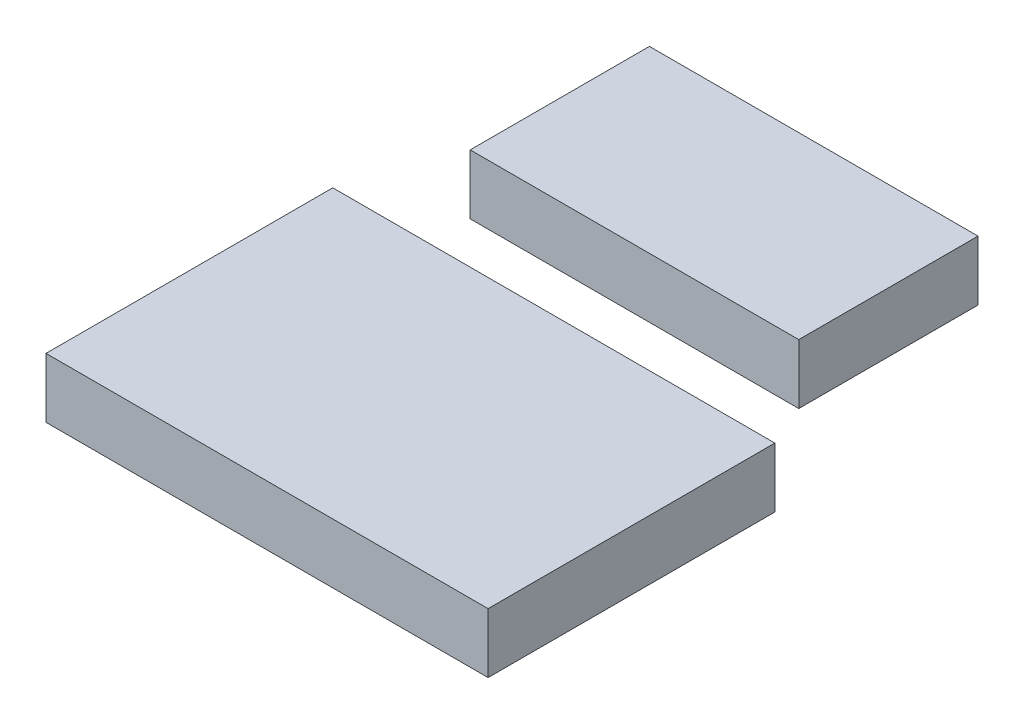
SolidWorks part; units mm, degrees
ref_plane "Front Plane" through (0, 0, 0) normal (0, 0, 1) x (1, 0, 0)
ref_plane "Top Plane" through (0, 0, 0) normal (0, 1, 0) x (1, 0, 0)
ref_plane "Right Plane" through (0, 0, 0) normal (1, 0, 0) x (0, 0, -1)
sketch "Sketch1" plane through (0, 0, 0) normal (0, 1, 0) x (1, 0, 0)
  line L0 (-31, 0.5) -> (-37, 0.5)
  line L1 (-37, 47.5) -> (37, 47.5)
  line L2 (-37, 47.5) -> (-37, -47.5)
  line L3 (-37, -47.5) -> (37, -47.5)
  line L4 (37, 47.5) -> (37, -47.5)
  line L5 (-37, 47.5) -> (37, -47.5) construction
  line L6 (-37, -47.5) -> (37, 47.5) construction
  line L7 (-31, 47.5) -> (24, 47.5)
  line L8 (-31, 47.5) -> (-31, 0.5)
  line L9 (-31, 0.5) -> (24, 0.5)
  line L10 (24, 47.5) -> (24, 0.5)
  line L11 (-31, 47.5) -> (24, 47.5)
  line L12 (-31, 47.5) -> (-31, 17.5)
  line L13 (-31, 17.5) -> (24, 17.5)
  line L14 (24, 47.5) -> (24, 17.5)
  line L15 (24, 0.5) -> (37, 0.5)
  point P0 (0, 0)
  dimension "D1" = 95
  dimension "D2" = 74
  dimension "D3" = 48
  dimension "D4" = 55
  dimension "D5" = 6
  dimension "D6" = 30
extrude "Boss-Extrude1" add sketch "Sketch1" along normal blind 10 contours L15 L9 L0 L2 L3 L4 | L8 L13 L10 L1
